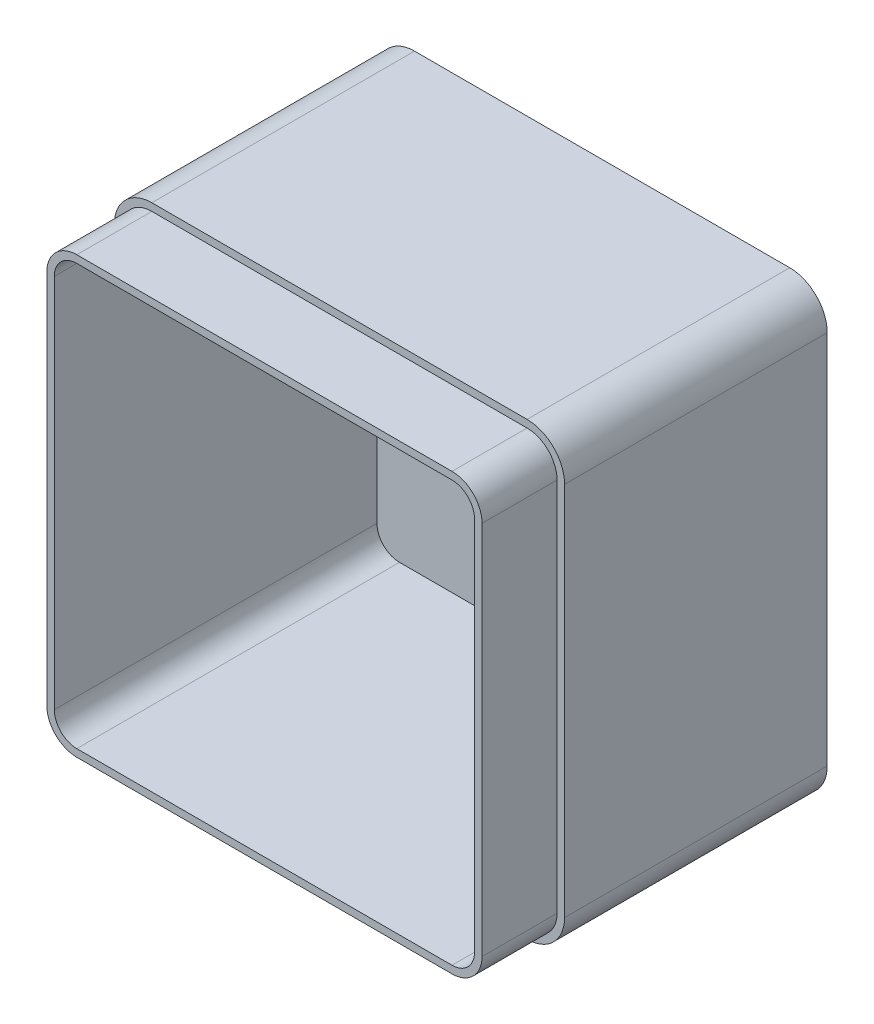
SolidWorks part; units mm, degrees
ref_plane "Front Plane" through (0, 0, 0) normal (0, 0, 1) x (1, 0, 0)
ref_plane "Top Plane" through (0, 0, 0) normal (0, 1, 0) x (1, 0, 0)
ref_plane "Right Plane" through (0, 0, 0) normal (1, 0, 0) x (0, 0, -1)
sketch "Sketch1" plane through (0, 0, 0) normal (0, 0, 1) x (1, 0, 0)
  line L1 (-60, 60) -> (60, 60)
  line L2 (-60, 60) -> (-60, -60)
  line L3 (-60, -60) -> (60, -60)
  line L4 (60, 60) -> (60, -60)
  line L5 (-60, 60) -> (60, -60) construction
  line L6 (-60, -60) -> (60, 60) construction
  point P0 (0, 0)
  dimension "D1" = 120
  dimension "D2" = 120
extrude "Boss-Extrude1" add sketch "Sketch1" along normal blind 90
fillet "Fillet1" radius 10 4 edges at (-60, -60, 45) (60, -60, 45) (-60, 60, 45) (60, 60, 45)
shell "Shell1" thickness 4
sketch "Sketch2" plane through (0, 0, 90) normal (0, 0, 1) x (1, 0, 0)
  line L0 (-58, 50) -> (-58, -50)
  line L1 (-50, -58) -> (50, -58)
  line L2 (58, -50) -> (58, 50)
  line L3 (50, 58) -> (-50, 58)
  line L4 (-60, 50) -> (-60, -50)
  line L5 (-50, -60) -> (50, -60)
  line L6 (60, -50) -> (60, 50)
  line L7 (50, 60) -> (-50, 60)
  line L8 (-60, 50) -> (-60, -50)
  line L9 (-50, -60) -> (50, -60)
  line L10 (60, -50) -> (60, 50)
  line L11 (50, 60) -> (-50, 60)
  arc A0 (-58, -50) -> (-50, -58) centre (-50, -50) ccw
  arc A1 (50, -58) -> (58, -50) centre (50, -50) ccw
  arc A2 (58, 50) -> (50, 58) centre (50, 50) ccw
  arc A3 (-50, 58) -> (-58, 50) centre (-50, 50) ccw
  arc A4 (-60, -50) -> (-50, -60) centre (-50, -50) ccw
  arc A5 (50, -60) -> (60, -50) centre (50, -50) ccw
  arc A6 (60, 50) -> (50, 60) centre (50, 50) ccw
  arc A7 (-50, 60) -> (-60, 50) centre (-50, 50) ccw
  arc A8 (-60, -50) -> (-50, -60) centre (-50, -50) ccw
  arc A9 (50, -60) -> (60, -50) centre (50, -50) ccw
  arc A10 (60, 50) -> (50, 60) centre (50, 50) ccw
  arc A11 (-50, 60) -> (-60, 50) centre (-50, 50) ccw
  dimension "D1" = 0
  dimension "D2" = 2
extrude "Cut-Extrude1" cut sketch "Sketch2" against normal blind 20
